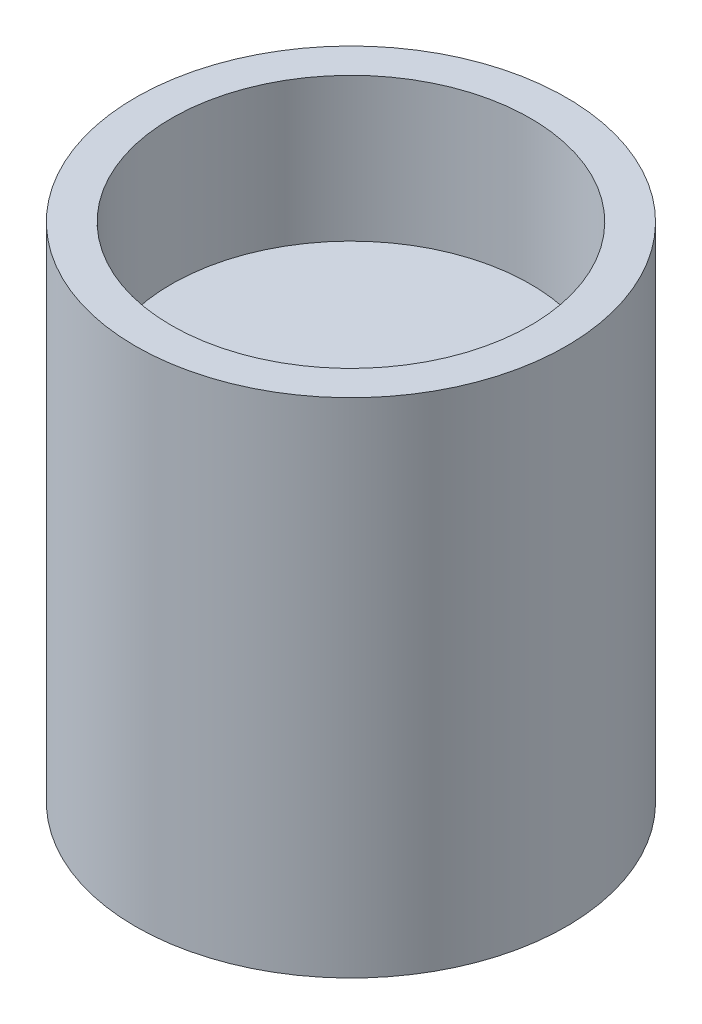
SolidWorks part; units mm, degrees
ref_plane "前视基准面" through (0, 0, 0) normal (0, 0, 1) x (1, 0, 0)
ref_plane "上视基准面" through (0, 0, 0) normal (0, 1, 0) x (1, 0, 0)
ref_plane "右视基准面" through (0, 0, 0) normal (1, 0, 0) x (0, 0, -1)
sketch "草图1" plane through (0, 0, 0) normal (0, 1, 0) x (1, 0, 0)
  circle A1 centre (0, 0) radius 3
  point P4 (0, 0)
  dimension "D3" = 6
extrude "凸台-拉伸1" add sketch "草图1" along normal blind 7
sketch "草图4" plane through (0, 0, 0) normal (0, 1, 0) x (1, 0, 0)
  line L0 (0.8292, 1.25) -> (0.8292, -1.25)
  circle A0 centre (0, 0) radius 1.5
  dimension "D2" = 3
  dimension "D1" = 2.5
extrude "切除-拉伸1" cut sketch "草图4" along normal blind 2.5 contours L0 A0
ref_plane "基准面2" through (0, 7, 0) normal (0, 1, 0) x (1, 0, 0)
sketch "草图5" plane through (0, 7, 0) normal (0, 1, 0) x (1, 0, 0)
  circle A0 centre (0, 0) radius 2.5
  dimension "D1" = 5
extrude "切除-拉伸2" cut sketch "草图5" against normal blind 2
